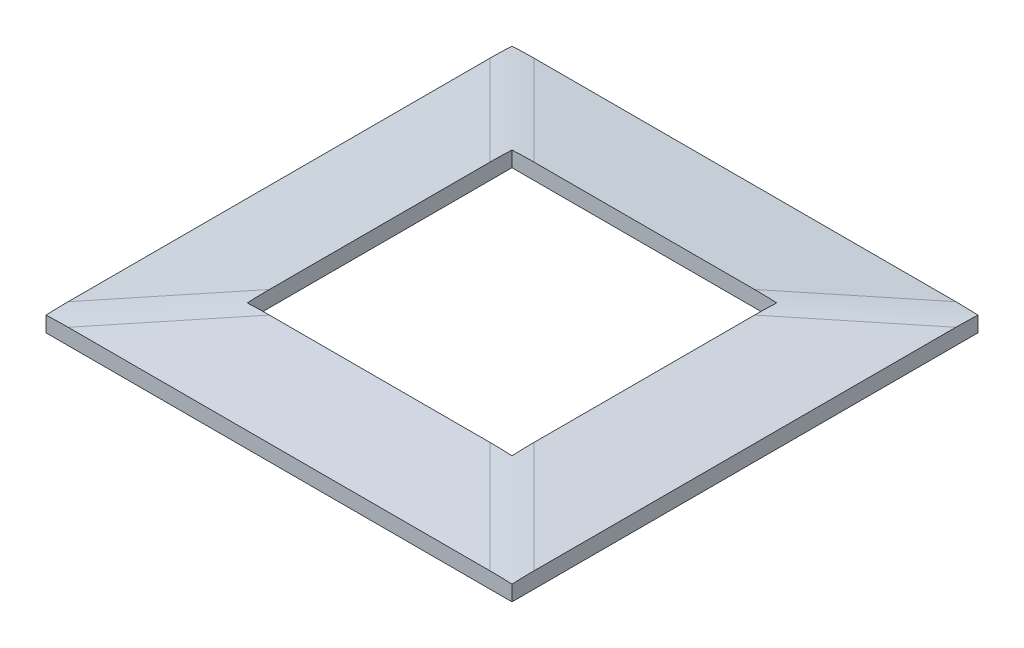
SolidWorks part; units mm, degrees
ref_plane "Спереди" through (0, 0, 0) normal (0, 0, 1) x (1, 0, 0)
ref_plane "Сверху" through (0, 0, 0) normal (0, 1, 0) x (1, 0, 0)
ref_plane "Справа" through (0, 0, 0) normal (1, 0, 0) x (0, 0, -1)
sketch "Эскиз1" plane through (0, 0, 0) normal (1, 0, 0) x (0, 0, -1)
  line L0 (44, 0) -> (-44, 0)
  line L1 (-44, 0) -> (-44, 3)
  line L2 (-44, 3) -> (-25, 5)
  line L3 (-25, 5) -> (25, 5)
  line L4 (0, 32.0992) -> (0, -19.2595) construction
  line L5 (44, 3) -> (25, 5)
  line L6 (44, 0) -> (44, 3)
  point P7 (0, 5)
  point P9 (0, 0)
extrude "Бобышка-Вытянуть1" add sketch "Эскиз1" along normal mid plane 88
sketch "Эскиз2" plane through (0, 0, 0) normal (0, 0, 1) x (1, 0, 0)
  line L0 (0, 27.9095) -> (0, -12.8469) construction
  line L1 (44, 0) -> (-44, 0)
  line L2 (-44, 0) -> (-44, 3)
  line L3 (-44, 3) -> (-25, 5)
  line L4 (44, 5) -> (-44, 5) construction
  line L5 (-25, 5) -> (25, 5)
  line L6 (44, 3) -> (25, 5)
  line L7 (44, 0) -> (44, 3)
  point P12 (0, 5)
  point P17 (0, 0)
extrude "Вырез-Вытянуть1" cut sketch "Эскиз2" against normal mid plane 88 flip side to cut
sketch "Эскиз3" plane through (0, 0, 0) normal (0, -1, 0) x (1, 0, 0)
  line L1 (-41.5, 42.0556) -> (41.5, 42.0556)
  line L2 (-41.5, 42.0556) -> (-41.5, -42.0556)
  line L3 (-41.5, -42.0556) -> (41.5, -42.0556)
  line L4 (41.5, 42.0556) -> (41.5, -42.0556)
  line L5 (-41.5, 42.0556) -> (41.5, -42.0556) construction
  line L6 (-41.5, -42.0556) -> (41.5, 42.0556) construction
  point P0 (0, 0)
extrude "Вырез-Вытянуть2" cut sketch "Эскиз3" against normal blind 2
sketch "Эскиз5" plane through (0, 0, 0) normal (0, -1, 0) x (1, 0, 0)
  line L1 (-25, 25) -> (25, 25)
  line L2 (-25, 25) -> (-25, -25)
  line L3 (-25, -25) -> (25, -25)
  line L4 (25, 25) -> (25, -25)
  line L5 (-25, 25) -> (25, -25) construction
  line L6 (-25, -25) -> (25, 25) construction
  point P0 (0, 0)
extrude "Вырез-Вытянуть3" cut sketch "Эскиз5" against normal through all
fillet "Скругление1" radius 40 4 edges at (34.5, 4, -34.5) (-34.5, 4, -34.5) (-34.5, 4, 34.5) (34.5, 4, 34.5)
